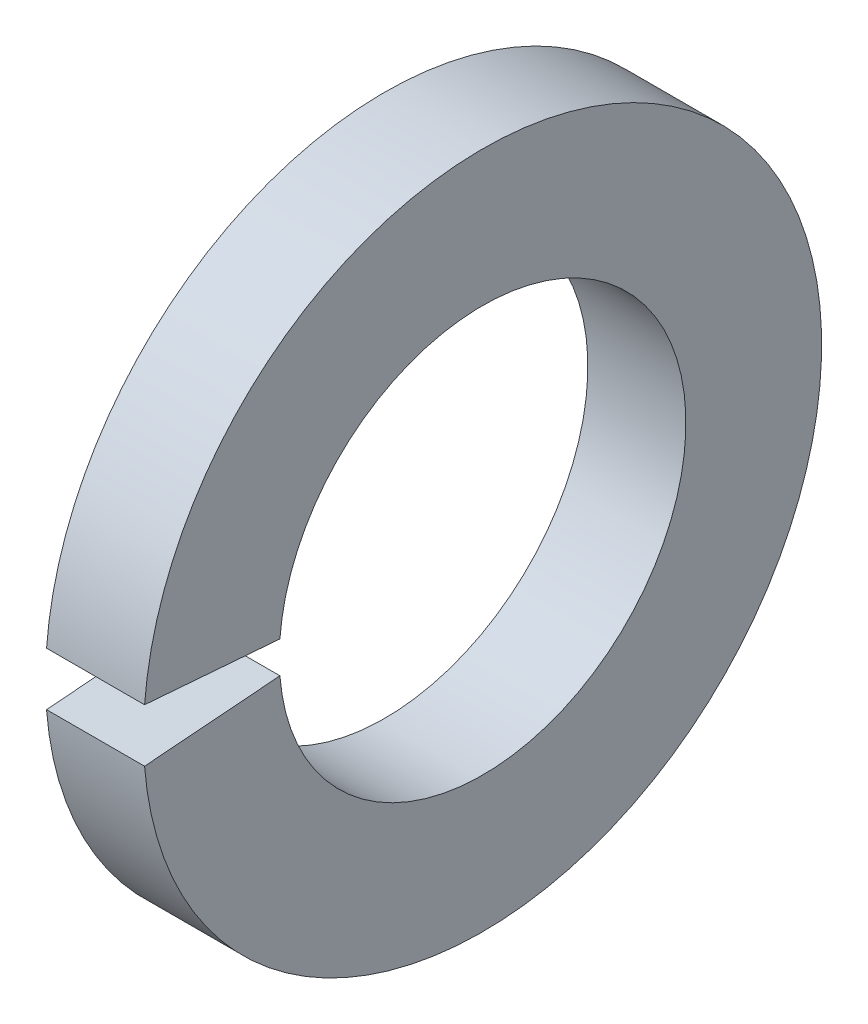
SolidWorks part; units mm, degrees
material "AISI Type 316L stainless steel"
ref_plane "Plane1" through (0, 0, 0) normal (0, 0, 1) x (1, 0, 0)
ref_plane "Plane2" through (0, 0, 0) normal (0, 1, 0) x (1, 0, 0)
ref_plane "Plane3" through (0, 0, 0) normal (1, 0, 0) x (0, 0, -1)
sketch "Sketch1" plane through (0, 0, 0) normal (0, 0, 1) x (1, 0, 0)
  line L0 (-34.925, 0) -> (9.525, 0) construction
  line L1 (0, 8.2169) -> (0, 13.7033)
  line L2 (0, 13.7033) -> (-3.9624, 13.7033)
  line L3 (-3.9624, 13.7033) -> (-3.9624, 8.2169)
  line L4 (-3.9624, 8.2169) -> (0, 8.2169)
  dimension "Thickness" = 3.9624
  dimension "Inside_dia" = 16.4338
  dimension "Outside_dia" = 27.4066
revolve "Base-Revolve" add sketch "Sketch1" angle 360 about L0
sketch "Sketch2" plane through (0, 0, 0) normal (-1, 0, 0) x (0, -1, 0)
  line L0 (0, 0) -> (1.0967, 13.9343)
  line L1 (0, -3.175) -> (0, 12.7) construction
  line L2 (0, 0) -> (-1.0967, 13.9343)
  arc A0 (1.0967, 13.9343) -> (-1.0967, 13.9343) centre (0, 0) ccw
  dimension "Gap_ang" = 9
  dimension "D1" = 13.9774
extrude "Gap" cut sketch "Sketch2" along normal through all
equation "\"D1@Sketch2\" = \"Outside_dia@Sketch1\" * 0.51"
